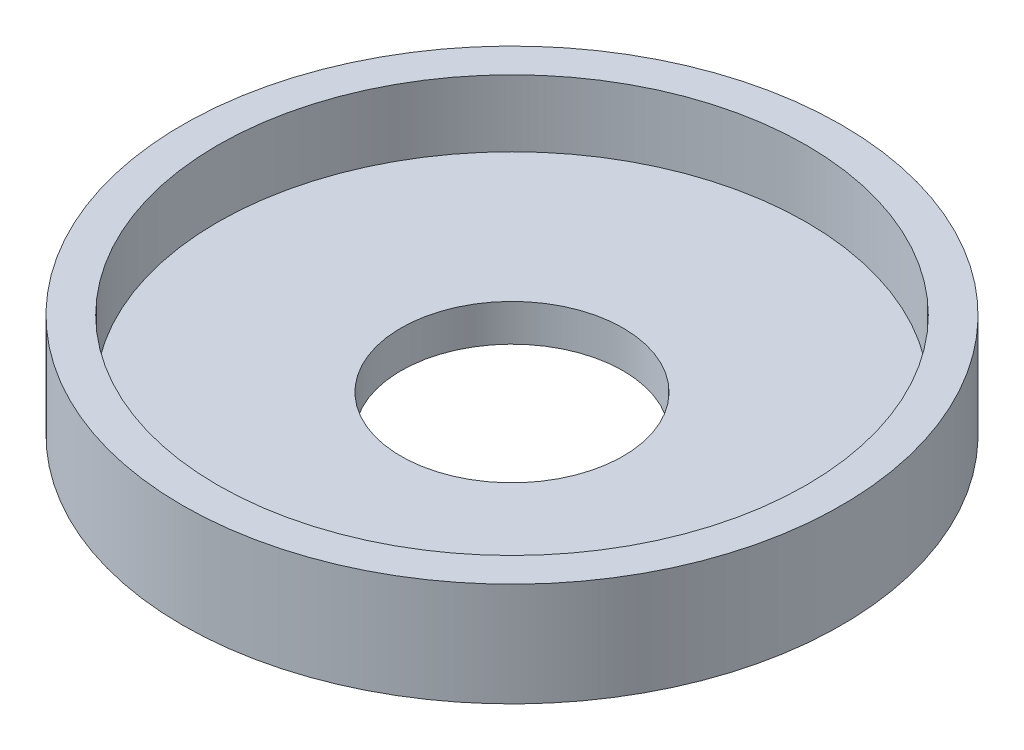
SolidWorks part; units mm, degrees
material "1.4301 (X5CrNi18-10)"
ref_plane "Vorne" through (0, 0, 0) normal (0, 0, 1) x (1, 0, 0)
ref_plane "Oben" through (0, 0, 0) normal (0, 1, 0) x (1, 0, 0)
ref_plane "Rechts" through (0, 0, 0) normal (1, 0, 0) x (0, 0, -1)
sketch "Skizze1" plane through (0, 0, 0) normal (1, 0, 0) x (0, 0, -1)
  line L0 (-6, 0) -> (-17.8, 0)
  line L1 (-17.8, 0) -> (-17.8, 5.6)
  line L2 (-17.8, 5.6) -> (-15.9, 5.6)
  line L3 (-15.9, 5.6) -> (-15.9, 2)
  line L4 (-15.9, 2) -> (-6, 2)
  line L5 (-6, 2) -> (-6, 0)
  line L6 (0, 0) -> (0, 5.6) construction
  dimension "D1" = 17.8
  dimension "D2" = 2
  dimension "D3" = 6
  dimension "D4" = 15.9
  dimension "D5" = 3.6
revolve "Rotation1" add sketch "Skizze1" angle 360 about L6
